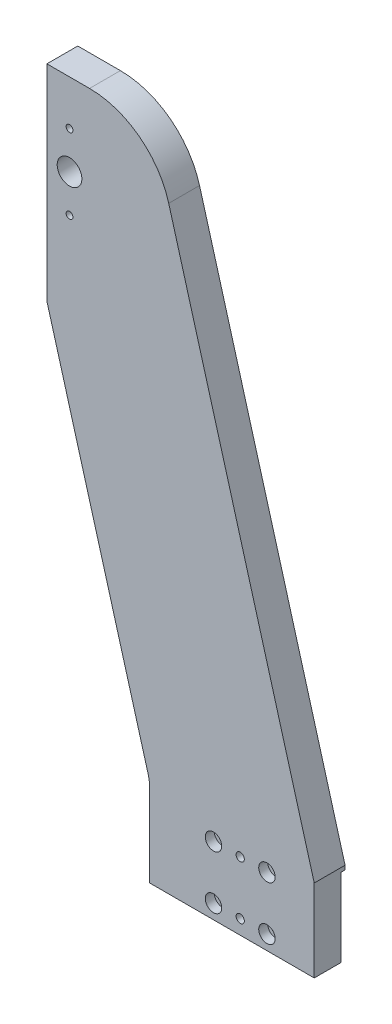
SolidWorks part; units mm, degrees
material "3.3547 (EN-AW 5083)"
ref_plane "Alzado" through (0, 0, 0) normal (0, 0, 1) x (1, 0, 0)
ref_plane "Planta" through (0, 0, 0) normal (0, 1, 0) x (1, 0, 0)
ref_plane "Vista lateral" through (0, 0, 0) normal (1, 0, 0) x (0, 0, -1)
sketch "Croquis1" plane through (0, 0, 0) normal (0, 0, 1) x (1, 0, 0)
  line L0 (80, 0) -> (80, 40)
  line L1 (-50, 320) -> (-29.2688, 320)
  line L2 (-50, 320) -> (-50, 220)
  line L3 (0, 0) -> (80, 0)
  line L4 (9.2285, 290.8607) -> (80, 40)
  line L9 (-50, 220) -> (-0.7513, 45.4303)
  line L11 (0, 40) -> (0, 0)
  arc A2 (9.2285, 290.8607) -> (-29.2688, 320) centre (-29.2688, 280) ccw
  arc A3 (0, 40) -> (-0.7513, 45.4303) centre (-20, 40) ccw
  point P14 (0, 42.7671)
  dimension "D7" = 20
  dimension "D9" = 40
  dimension "D1" = 40
  dimension "D2" = 320
  dimension "D3" = 80
  dimension "D4" = 50
  dimension "D5" = 100
  dimension "D6" = 40
extrude "Saliente-Extruir1" add sketch "Croquis1" along normal blind 15
sketch "Croquis2" plane through (0, 0, 0) normal (0, 0, -1) x (-1, 0, 0)
  line L0 (29.2688, 320) -> (50, 320) construction
  line L2 (50, 320) -> (50, 220) construction
  circle A0 centre (39, 280) radius 6
  dimension "D3" = 12
  dimension "D1" = 40
  dimension "D2" = 11
extrude "Cortar-Extruir1" cut sketch "Croquis2" against normal through all
hole_wizard "Perforador para roscar para macho de roscar para M44" positions "Croquis7" profile "Croquis8" hole size "M4" standard "DIN"
sketch "Croquis7" plane through (0, 0, 15) normal (0, 0, 1) x (1, 0, 0)
  line L0 (-39, 298.25) -> (-39, 261.75)
  circle A0 centre (-39, 280) radius 6 construction
  point P1 (-39, 298.25)
  point P2 (-39, 261.75)
  dimension "D1" = 18.25
  dimension "D2" = 18.25
sketch "Croquis8" plane through (-39, 298.25, 15) normal (1, 0, 0) x (0, -1, 0)
  line L0 (0, 0) -> (0, 7.9914)
  line L1 (0, 7.9914) -> (1.65, 7)
  line L2 (1.65, 7) -> (1.65, 0)
  line L5 (1.65, 0) -> (0, 0)
  line L10 (0, 7.9914) -> (-1.65, 7) construction
  line L11 (0, -6.35) -> (0, 107.95) construction
  dimension "Diámetro de taladro" = 3.3
  dimension "Profundidad de taladro" = 7
  dimension "Ángulo de perforador" = 118
sketch "Croquis9" plane through (0, 0, 0) normal (0, 0, -1) x (-1, 0, 0)
  line L1 (0, 0) -> (-80, 0)
  line L2 (0, 0) -> (0, 38)
  line L3 (0, 38) -> (-80, 38)
  line L4 (-80, 0) -> (-80, 38)
  dimension "D1" = 80
  dimension "D2" = 38
extrude "Cortar-Extruir2" cut sketch "Croquis9" against normal blind 2
hole_wizard "Taladro roscado M41" positions "Croquis10" profile "Croquis11" tap size "M4" standard "DIN"
sketch "Croquis10" plane through (-50, 0, 0) normal (-1, 0, 0) x (0, 0, 1)
  line L0 (15, 320) -> (0, 320) construction
  line L1 (15, 320) -> (15, 220) construction
  line L2 (0, 240) -> (15, 240) construction
  line L3 (0, 320) -> (0, 220) construction
  line L5 (9, 320) -> (9, 240) construction
  point P0 (9, 312)
  point P2 (9, 248)
  point P9 (9, 291)
  point P11 (9, 269)
  point P24 (9, 312)
  point P25 (9, 301.4664)
  point P26 (0, 0)
  point P27 (9, 265.325)
  point P28 (9, 255)
  point P29 (9, 240)
  dimension "D1" = 8
  dimension "D2" = 8
  dimension "D3" = 6
  dimension "D4" = 29
  dimension "D5" = 80
  dimension "D6" = 29
sketch "Croquis11" plane through (-50, 312, 9) normal (0, 1, 0) x (0, 0, 1)
  line L0 (0, 0) -> (0, 15.9914)
  line L1 (0, 15.9914) -> (1.65, 15)
  line L2 (1.65, 15) -> (1.65, 0)
  line L5 (1.65, 0) -> (0, 0)
  line L10 (0, 15.9914) -> (-1.65, 15) construction
  line L11 (0, -6.35) -> (0, 107.95) construction
  dimension "Diámetro de perforador para roscar" = 3.3
  dimension "Profundidad de perforador para roscar" = 15
  dimension "Ángulo de perforador" = 118
cosmetic thread "Rosca de taladro1" parameters "D1"=8, "D2"=4
cosmetic thread "Rosca de taladro2" parameters "D1"=8, "D2"=4
cosmetic thread "Rosca de taladro3" parameters "D1"=8, "D2"=4
cosmetic thread "Rosca de taladro4" parameters "D1"=8, "D2"=4
hole_wizard "Taladros de espiga de Ø4.0mm1" positions "Croquis12" profile "Croquis13" hole size "Ø4.0" standard "DIN"
sketch "Croquis12" plane through (-50, 0, 0) normal (-1, 0, 0) x (0, 0, 1)
  line L0 (15, 320) -> (0, 320) construction
  line L1 (15, 320) -> (15, 220) construction
  point P0 (9, 304)
  point P2 (9, 256)
  dimension "D1" = 16
  dimension "D2" = 64
  dimension "D3" = 6
  dimension "D4" = 6
sketch "Croquis13" plane through (-50, 304, 9) normal (0, 1, 0) x (0, 0, 1)
  line L0 (0, 0) -> (0, 18.2017)
  line L1 (0, 18.2017) -> (2, 17)
  line L2 (2, 17) -> (2, 0)
  line L5 (2, 0) -> (0, 0)
  line L10 (0, 18.2017) -> (-2, 17) construction
  line L11 (0, -6.35) -> (0, 107.95) construction
  dimension "Diámetro de taladro" = 4
  dimension "Profundidad de taladro" = 17
  dimension "Ángulo de perforador" = 118
hole_wizard "Taladros de espiga de Ø4.0mm3" positions "Croquis14" profile "Croquis15" hole size "Ø4.0" standard "DIN" end condition through all
sketch "Croquis14" plane through (0, 0, 15) normal (0, 0, 1) x (1, 0, 0)
  line L0 (44, 33) -> (44, 7) construction
  line L3 (0, 0) -> (80, 0) construction
  line L4 (80, 0) -> (80, 40) construction
  point P1 (44, 33)
  point P2 (44, 7)
  dimension "D1" = 26
  dimension "D2" = 7
  dimension "D3" = 36
sketch "Croquis15" plane through (44, 33, 15) normal (1, 0, 0) x (0, -1, 0)
  line L0 (0, 0) -> (0, 15)
  line L1 (0, 15) -> (2, 15)
  line L2 (2, 15) -> (2, 0)
  line L5 (2, 0) -> (0, 0)
  line L11 (0, -6.35) -> (0, 107.95) construction
  dimension "Diámetro de taladro hasta el siguiente" = 4
  dimension "Profundidad de taladro hasta el siguiente" = 15
hole_wizard "Refrentado para tornillo con cabeza hueca de M41" positions "Croquis16" profile "Croquis17" counterbore size "M4" standard "DIN" end condition through all
sketch "Croquis16" plane through (0, 0, 15) normal (0, 0, 1) x (1, 0, 0)
  line L1 (31, 7) -> (57, 7)
  line L2 (31, 7) -> (31, 33)
  line L3 (31, 33) -> (57, 33)
  line L4 (57, 7) -> (57, 33)
  line L5 (31, 7) -> (57, 33) construction
  line L6 (31, 33) -> (57, 7) construction
  line L7 (0, 0) -> (80, 0) construction
  line L8 (80, 0) -> (80, 40) construction
  point P2 (57, 33)
  point P135 (31, 7)
  point P136 (31, 33)
  point P137 (57, 7)
  dimension "D1" = 26
  dimension "D2" = 26
  dimension "D3" = 7
  dimension "D4" = 23
sketch "Croquis17" plane through (57, 33, 15) normal (1, 0, 0) x (0, -1, 0)
  line L0 (0, 0) -> (0, 15)
  line L1 (0, 15) -> (2.25, 15)
  line L3 (2.25, 15) -> (2.25, 4.4)
  line L4 (2.25, 4.4) -> (4, 4.4)
  line L5 (4, 4.4) -> (4, 0)
  line L7 (4, 0) -> (0, 0)
  line L11 (0, -6.35) -> (0, 107.95) construction
  dimension "Diámetro de taladro hasta el siguiente" = 4.5
  dimension "Profundidad de taladro hasta el siguiente" = 15
  dimension "Diámetro de refrentado" = 8
  dimension "Profundidad de refrentado" = 4.4
